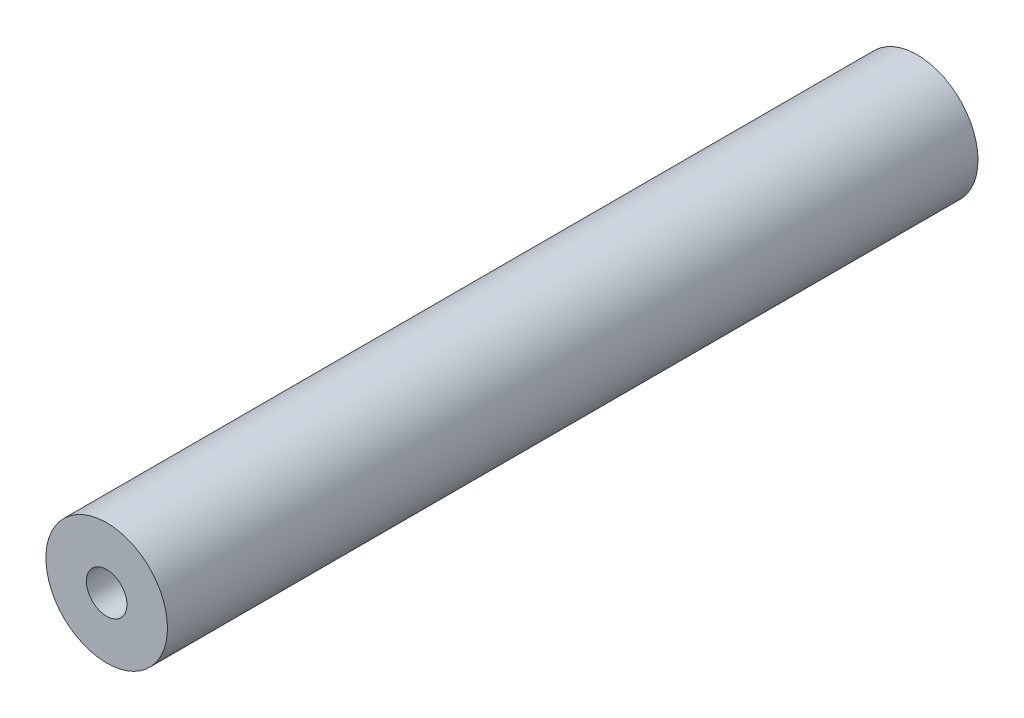
SolidWorks part; units mm, degrees
ref_plane "Piano frontale" through (0, 0, 0) normal (0, 0, 1) x (1, 0, 0)
ref_plane "Piano superiore" through (0, 0, 0) normal (0, 1, 0) x (1, 0, 0)
ref_plane "Piano destro" through (0, 0, 0) normal (1, 0, 0) x (0, 0, -1)
sketch "Schizzo1" plane through (0, 0, 0) normal (0, 0, 1) x (1, 0, 0)
  circle A0 centre (0, 0) radius 1.5
  circle A1 centre (0, 0) radius 0.5
  dimension "D1" = 1
  dimension "D2" = 3
extrude "Estrusione-Estrusione1" add sketch "Schizzo1" along normal blind 20
